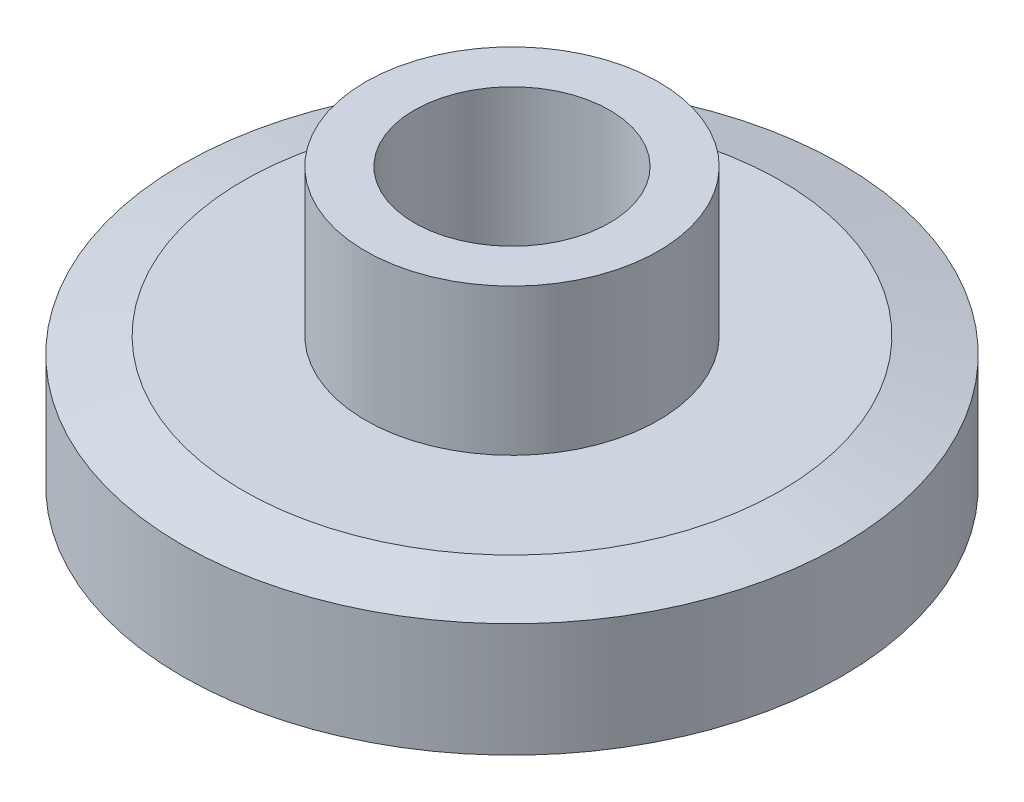
SolidWorks part; units mm, degrees
material "Сталь ШХ15 ГОСТ 801-78"
ref_plane "Plane1" through (0, 0, 0) normal (0, 0, 1) x (1, 0, 0)
ref_plane "Plane2" through (0, 0, 0) normal (0, 1, 0) x (1, 0, 0)
ref_plane "Plane3" through (0, 0, 0) normal (1, 0, 0) x (0, 0, -1)
sketch "Эскиз2" plane through (0, 0, 0) normal (0, 0, 1) x (1, 0, 0)
  line L0 (0, 0) -> (6.75, 0)
  line L1 (6.75, 0) -> (6.75, 3)
  line L2 (6.75, 3) -> (3, 3)
  line L3 (3, 3) -> (3, 6)
  line L4 (3, 6) -> (0, 6)
  line L5 (0, 6) -> (0, 0)
  dimension "D1" = 6.75
  dimension "D2" = 3
  dimension "D3" = 3
  dimension "D4" = 3
ref_axis "Ось1" through (0, 6, 0) along (0, -1, 0)
revolve "Повернуть2" add sketch "Эскиз2" angle 360 about axis through (0, 6, 0) along (0, -1, 0)
chamfer "Фаска2" distance 1.25 angle 15 1 edges at (-6.75, 3, 0)
chamfer "Фаска3" distance 1.25 angle 15 1 edges at (-6.75, 0, 0)
sketch "Эскиз4" plane through (0, 6, 0) normal (0, 1, 0) x (1, 0, 0)
  circle A0 centre (0, 0) radius 2
  dimension "D1" = 4
extrude "Вырез-Вытянуть2" cut sketch "Эскиз4" against normal through all both contours A0
